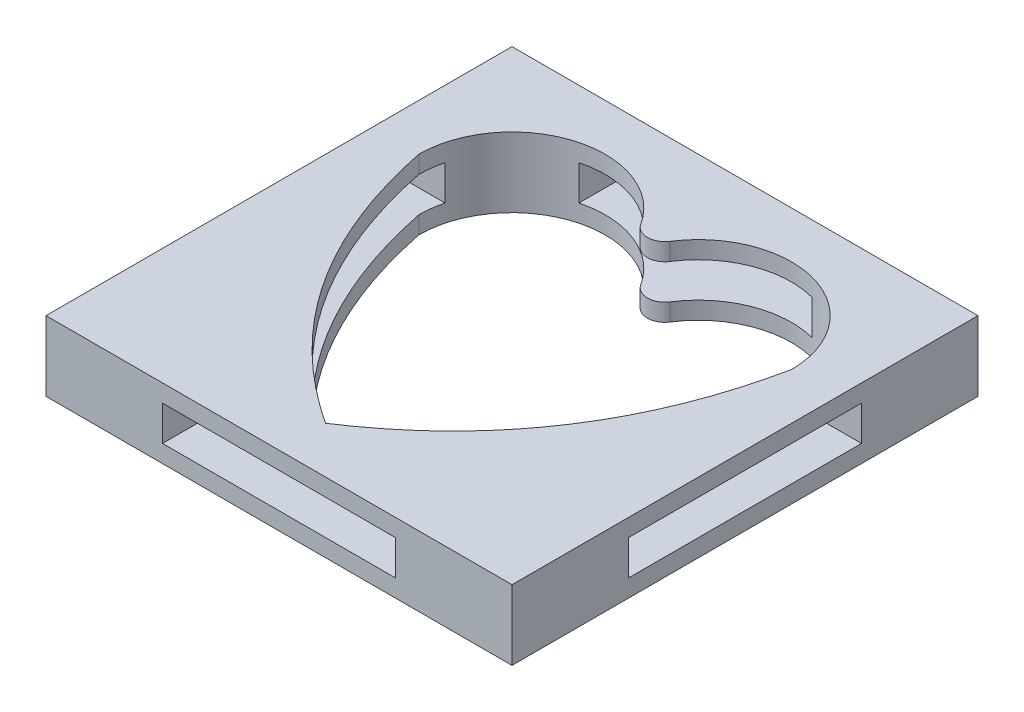
SolidWorks part; units mm, degrees
ref_plane "Front Plane" through (0, 0, 0) normal (0, 0, 1) x (1, 0, 0)
ref_plane "Top Plane" through (0, 0, 0) normal (0, 1, 0) x (1, 0, 0)
ref_plane "Right Plane" through (0, 0, 0) normal (1, 0, 0) x (0, 0, -1)
sketch "Sketch1" plane through (0, 0, 0) normal (0, 1, 0) x (1, 0, 0)
  line L0 (0, 8) -> (0, 4) construction
  line L1 (10, -10) -> (-10, -10)
  line L2 (10, -10) -> (10, 10)
  line L3 (10, 10) -> (-10, 10)
  line L4 (-10, -10) -> (-10, 10)
  line L5 (8, -8) -> (-8, -8) construction
  line L6 (8, -8) -> (8, 8) construction
  line L7 (8, 8) -> (-8, 8) construction
  line L8 (-8, -8) -> (-8, 8) construction
  line L9 (0, 4) -> (4, 4) construction
  line L10 (0, 4) -> (-4, 4) construction
  line L11 (0, -8) -> (0, -4.5) construction
  line L12 (0, -4.5) -> (-4, -4.5) construction
  line L13 (0, -4.5) -> (4, -4.5) construction
  arc A0 (-0.6316, 6.1573) -> (-8, 4) centre (-4, 4) ccw
  arc A1 (8, 4) -> (0.6316, 6.1573) centre (4, 4) ccw
  arc A2 (-0.6316, 6.1573) -> (0.6316, 6.1573) centre (0, 6.5617) ccw
  spline S0 degree 2 poles (-8, 4) (-6.4033, -3.8115) (0, -8) knots 0 0 0 1 1 1
  spline S1 degree 2 poles (8, 4) (6.4033, -3.8115) (0, -8) knots 0 0 0 1 1 1
  point P0 (0, 0)
  point P6 (0, 0)
  dimension "D3" = 0.75
  dimension "D1" = 20
  dimension "D2" = 20
  dimension "D4" = 16
  dimension "D5" = 4
  dimension "D6" = 4
  dimension "D8" = 3.5
  dimension "D9" = 4
  dimension "D10" = 4
extrude "Boss-Extrude1" add sketch "Sketch1" along normal blind 3
sketch "Sketch2" plane through (10, 0, 0) normal (1, 0, 0) x (0, 0, -1)
  line L0 (-10, 3) -> (-10, 0) construction
  line L1 (-5, 2.25) -> (5, 2.25)
  line L2 (-5, 2.25) -> (-5, 0.75)
  line L3 (-5, 0.75) -> (5, 0.75)
  line L4 (5, 2.25) -> (5, 0.75)
  line L5 (0, 0.75) -> (0, 2.25) construction
  line L6 (-5, 1.5) -> (5, 1.5) construction
  line L7 (-10, 3) -> (10, 3) construction
  point P0 (0, 1.5)
  dimension "D1" = 1.5
  dimension "D2" = 10
  dimension "D3" = 5
  dimension "D4" = 0.75
extrude "Cut-Extrude1" cut sketch "Sketch2" against normal through all
sketch "Sketch3" plane through (0, 0, 10) normal (0, 0, 1) x (1, 0, 0)
  line L0 (-10, 3) -> (-10, 0) construction
  line L1 (5, 0.75) -> (-5, 0.75)
  line L2 (5, 0.75) -> (5, 2.25)
  line L3 (5, 2.25) -> (-5, 2.25)
  line L4 (-5, 0.75) -> (-5, 2.25)
  line L5 (0, 2.25) -> (0, 0.75) construction
  line L6 (5, 1.5) -> (-5, 1.5) construction
  line L7 (-10, 3) -> (10, 3) construction
  point P0 (0, 1.5)
  dimension "D1" = 1.5
  dimension "D2" = 10
  dimension "D3" = 5
  dimension "D4" = 0.75
extrude "Cut-Extrude2" cut sketch "Sketch3" against normal through all
